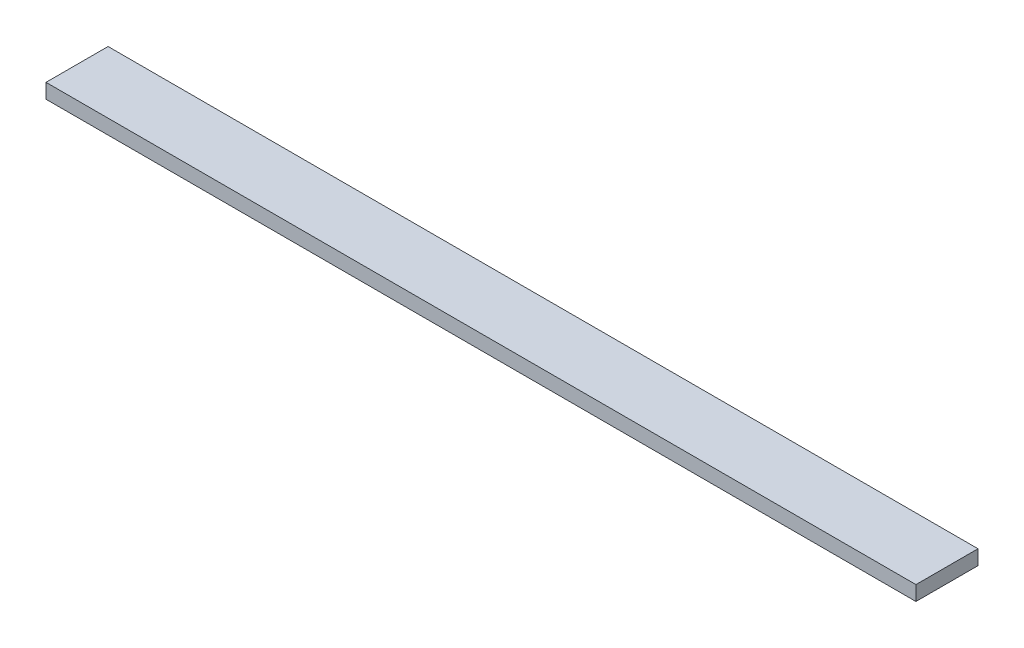
SolidWorks part; units mm, degrees
ref_plane "Front Plane" through (0, 0, 0) normal (0, 0, 1) x (1, 0, 0)
ref_plane "Top Plane" through (0, 0, 0) normal (0, 1, 0) x (1, 0, 0)
ref_plane "Right Plane" through (0, 0, 0) normal (1, 0, 0) x (0, 0, -1)
sketch "Sketch1" plane through (0, 0, 0) normal (0, 1, 0) x (1, 0, 0)
  line L1 (0, 0) -> (178, 0)
  line L2 (0, 0) -> (0, 12.7)
  line L3 (0, 12.7) -> (178, 12.7)
  line L4 (178, 0) -> (178, 12.7)
  dimension "D1" = 12.7
  dimension "D2" = 178
extrude "Boss-Extrude1" add sketch "Sketch1" along normal blind 3
